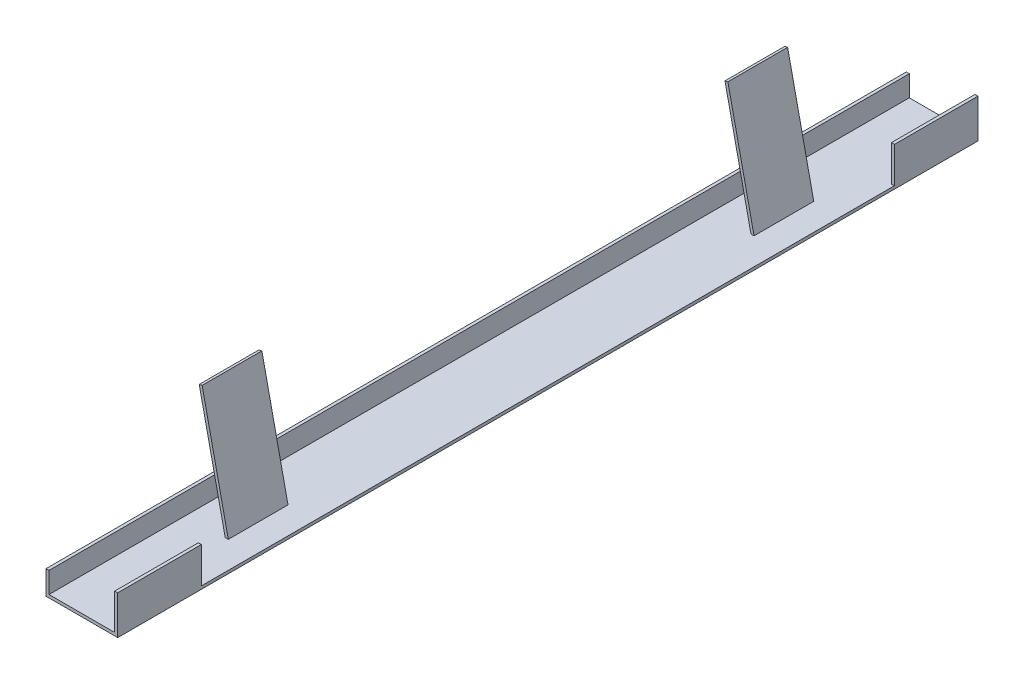
SolidWorks part; units mm, degrees
ref_plane "Front Plane" through (0, 0, 0) normal (0, 0, 1) x (1, 0, 0)
ref_plane "Top Plane" through (0, 0, 0) normal (0, 1, 0) x (1, 0, 0)
ref_plane "Right Plane" through (0, 0, 0) normal (1, 0, 0) x (0, 0, -1)
sketch "Sketch1" plane through (0, 0, 0) normal (0, 0, 1) x (1, 0, 0)
  line L0 (103.1875, 12.7) -> (103.1875, 0)
  line L1 (138.1125, 20.6375) -> (138.1125, 0)
  line L2 (101.6, 0) -> (101.6, 12.7)
  line L3 (139.7, 0) -> (139.7, 20.6375)
  line L4 (101.6, 0) -> (139.7, 0)
  line L5 (111.5498, 65.5267) -> (125.4496, 1.5875)
  line L6 (109.9985, 65.1895) -> (111.5498, 65.5267)
  line L7 (109.9985, 65.1895) -> (123.825, 1.5875)
  line L8 (101.6, 1.5875) -> (139.7, 1.5875)
  line L9 (139.7, 20.6375) -> (138.1125, 20.6375)
  line L10 (101.6, 12.7) -> (103.1875, 12.7)
sketch "Sketch2" plane through (0, 0, 0) normal (0, 0, 1) x (1, 0, 0)
  line L0 (101.6, 12.7) -> (101.6, 0)
  line L1 (101.6, 0) -> (139.7, 0)
  line L2 (139.7, 0) -> (139.7, 20.6375)
  line L3 (139.7, 20.6375) -> (138.1125, 20.6375)
  line L4 (138.1125, 20.6375) -> (138.1125, 1.5875)
  line L5 (138.1125, 20.6375) -> (138.1125, 0) construction
  line L6 (138.1125, 1.5875) -> (125.4496, 1.5875)
  line L7 (125.4496, 1.5875) -> (111.5498, 65.5267)
  line L8 (111.5498, 65.5267) -> (109.9985, 65.1895)
  line L9 (109.9985, 65.1895) -> (123.825, 1.5875)
  line L10 (123.825, 1.5875) -> (103.1875, 1.5875)
  line L11 (103.1875, 12.7) -> (103.1875, 0) construction
  line L12 (101.6, 1.5875) -> (139.7, 1.5875) construction
  line L13 (103.1875, 1.5875) -> (103.1875, 12.7)
  line L14 (103.1875, 12.7) -> (101.6, 12.7)
extrude "Extrude1" add sketch "Sketch2" along normal mid plane 457.2
sketch "Sketch3" plane through (0, 0, 0) normal (0, 0, 1) x (1, 0, 0)
  line L0 (103.1875, 1.5875) -> (138.1125, 1.5875)
  line L1 (138.1125, 1.5875) -> (138.1125, 20.6375)
  line L2 (138.1125, 20.6375) -> (111.5498, 65.5267)
  line L3 (111.5498, 65.5267) -> (109.9985, 65.1895)
  line L4 (109.9985, 65.1895) -> (103.1875, 12.7)
  line L5 (103.1875, 12.7) -> (103.1875, 1.5875)
extrude "Cut-Extrude1" cut sketch "Sketch3" against normal mid plane 247.65
sketch "Sketch4" plane through (0, 0, 228.6) normal (0, 0, 1) x (1, 0, 0)
  line L0 (103.1875, 12.7) -> (103.1875, 1.5875)
  line L1 (103.1875, 1.5875) -> (138.1125, 1.5875)
  line L2 (138.1125, 1.5875) -> (138.1125, 20.6375)
  line L3 (138.1125, 20.6375) -> (111.5498, 65.5267)
  line L4 (111.5498, 65.5267) -> (109.9985, 65.1895)
  line L5 (109.9985, 65.1895) -> (103.1875, 12.7)
extrude "Cut-Extrude2" cut sketch "Sketch4" against normal blind 73.025
sketch "Sketch5" plane through (0, 0, -228.6) normal (0, 0, -1) x (-1, 0, 0)
  line L0 (-138.1125, 20.6375) -> (-138.1125, 1.5875)
  line L1 (-138.1125, 1.5875) -> (-103.1875, 1.5875)
  line L2 (-103.1875, 1.5875) -> (-103.1875, 12.7)
  line L3 (-103.1875, 12.7) -> (-109.9985, 65.1895)
  line L4 (-109.9985, 65.1895) -> (-111.5498, 65.5267)
  line L5 (-111.5498, 65.5267) -> (-138.1125, 20.6375)
extrude "Cut-Extrude3" cut sketch "Sketch5" against normal blind 73.025
sketch "Sketch6" plane through (0, 0, 0) normal (0, 0, 1) x (1, 0, 0)
  line L4 (138.1125, 1.5875) -> (139.7, 1.5875)
  line L5 (139.7, 0) -> (139.7, 20.6375) construction
  line L6 (139.7, 1.5875) -> (139.7, 20.6375)
  line L7 (139.7, 20.6375) -> (138.1125, 20.6375)
  line L8 (138.1125, 20.6375) -> (138.1125, 1.5875)
extrude "Cut-Extrude4" cut sketch "Sketch6" against normal mid plane 368.3
